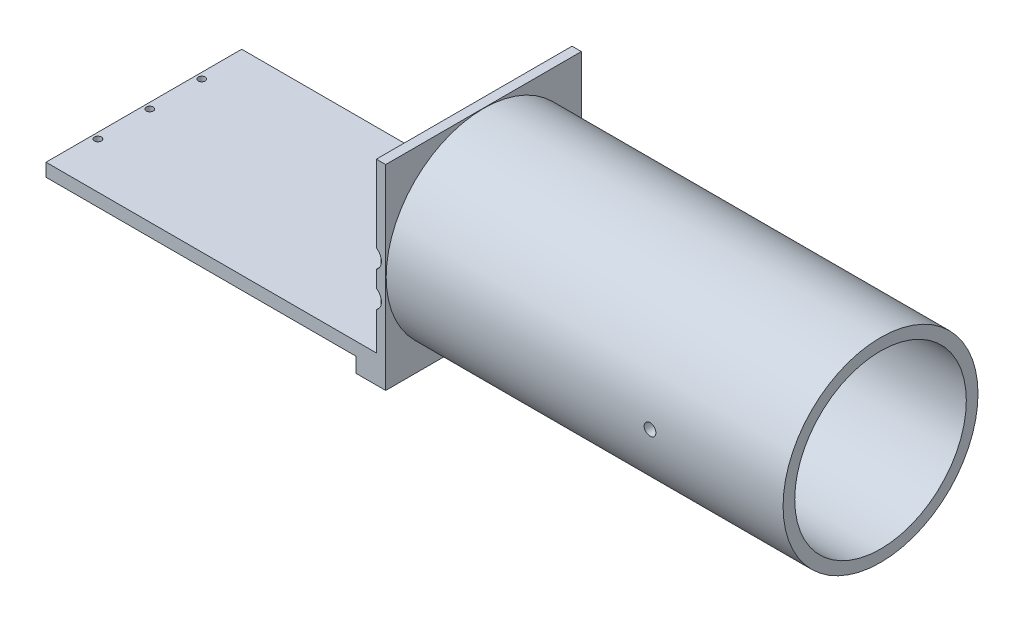
SolidWorks part; units mm, degrees
ref_plane "Front Plane" through (0, 0, 0) normal (0, 0, 1) x (1, 0, 0)
ref_plane "Top Plane" through (0, 0, 0) normal (0, 1, 0) x (1, 0, 0)
ref_plane "Right Plane" through (0, 0, 0) normal (1, 0, 0) x (0, 0, -1)
sketch "Sketch3" plane through (0, 0, 0) normal (0, 1, 0) x (1, 0, 0)
  line L0 (-38.8297, 34.4457) -> (-38.8297, -49.3743)
  line L1 (-38.8297, -49.3743) -> (106.6703, -49.3743)
  line L2 (106.6703, -49.3743) -> (106.6703, 34.4457)
  line L3 (106.6703, 34.4457) -> (-38.8297, 34.4457)
  dimension "D1" = 83.82
  dimension "D2" = 145.5
extrude "Boss-Extrude1" add sketch "Sketch3" along normal blind 83.82
sketch "Sketch4" plane through (0, 83.82, 0) normal (0, 1, 0) x (1, 0, 0)
  line L0 (-38.8297, 34.4457) -> (-38.8297, -44.8663)
  line L1 (-38.8297, 34.4457) -> (-38.8297, -49.3743) construction
  line L2 (-38.8297, -44.8663) -> (102.6703, -44.8663)
  line L3 (102.6703, -44.8663) -> (102.6703, 34.4457)
  line L4 (106.6703, 34.4457) -> (-38.8297, 34.4457) construction
  line L5 (102.6703, 34.4457) -> (-38.8297, 34.4457)
  dimension "D1" = 79.312
  dimension "D2" = 141.5
extrude "Cut-Extrude1" cut sketch "Sketch4" against normal blind 71.882
sketch "Sketch5" plane through (106.6703, 0, 0) normal (1, 0, 0) x (0, 0, -1)
  line L0 (-32.4113, 83.82) -> (-32.4113, 11.938) construction
  line L1 (-44.8663, 83.82) -> (34.4457, 83.82) construction
  line L2 (-44.8663, 11.938) -> (34.4457, 11.938) construction
  line L3 (-7.4113, 83.82) -> (-7.4113, 11.938) construction
  line L4 (17.5887, 83.82) -> (17.5887, 11.938) construction
  line L5 (34.4457, 54.438) -> (-44.8663, 54.438) construction
  line L6 (34.4457, 11.938) -> (34.4457, 83.82) construction
  line L7 (-44.8663, 11.938) -> (-44.8663, 83.82) construction
  line L8 (34.4457, 41.938) -> (-44.8663, 41.938) construction
  line L9 (34.4457, 29.438) -> (-44.8663, 29.438) construction
  line L10 (-44.8663, 11.938) -> (-44.8663, 83.82) construction
  line L11 (34.4457, 11.938) -> (-44.8663, 11.938) construction
  circle A0 centre (-7.4113, 41.938) radius 12.7
  dimension "D1" = 12.455
  dimension "D2" = 37.455
  dimension "D3" = 62.455
  dimension "D4" = 17.5
  dimension "D5" = 30
  dimension "D6" = 42.5
hole_wizard "CBORE for M3 Hex Head Cap Screw1" positions "Sketch6" profile "Sketch7" counterbore size "M3" standard "ISO" end condition up to next
sketch "Sketch6" plane through (106.6703, 0, 0) normal (1, 0, 0) x (0, 0, -1)
  line L0 (-32.4113, 83.82) -> (-32.4113, 11.938) construction
  line L1 (34.4457, 54.438) -> (-44.8663, 54.438) construction
  line L2 (17.5887, 83.82) -> (17.5887, 11.938) construction
  line L3 (34.4457, 29.438) -> (-44.8663, 29.438) construction
  point P0 (-32.4113, 54.438)
  point P6 (17.5887, 54.438)
  point P10 (17.5887, 29.438)
  point P14 (-32.4113, 29.438)
sketch "Sketch7" plane through (106.6703, 54.438, 32.4113) normal (0, 1, 0) x (0, 0, -1)
  line L0 (0, 0) -> (0, 4)
  line L1 (0, 4) -> (1.7, 4)
  line L3 (1.7, 4) -> (1.7, 2)
  line L4 (1.7, 2) -> (4.6755, 2)
  line L5 (4.6755, 2) -> (4.6755, 0)
  line L7 (4.6755, 0) -> (0, 0)
  line L11 (0, -6.35) -> (0, 107.95) construction
  dimension "Thru Hole Dia." = 3.4
  dimension "Thru Hole Depth" = 4
  dimension "C'Bore Dia." = 9.351
  dimension "C'Bore Depth" = 2
extrude "Cut-Extrude3" cut sketch "Sketch5" against normal up to next contours A0
sketch "Sketch8" plane through (0, 0, 49.3743) normal (0, 0, 1) x (1, 0, 0)
  line L0 (100.1703, 83.82) -> (100.1703, 11.938) construction
  line L1 (-38.8297, 83.82) -> (102.6703, 83.82) construction
  line L2 (102.6703, 11.938) -> (-38.8297, 11.938) construction
  line L3 (-36.3297, 83.82) -> (-36.3297, 11.938) construction
  line L4 (-38.8297, 11.938) -> (102.6703, 11.938) construction
  line L5 (102.6703, 46.938) -> (-38.8297, 46.938) construction
  line L6 (102.6703, 11.938) -> (102.6703, 83.82) construction
  line L7 (-38.8297, 11.938) -> (-38.8297, 83.82) construction
  line L8 (102.6703, 31.938) -> (-38.8297, 31.938) construction
  line L9 (102.6703, 11.938) -> (102.6703, 83.82) construction
  dimension "D1" = 2.5
  dimension "D2" = 139
  dimension "D3" = 20
  dimension "D4" = 35
hole_wizard "CBORE for M3 Hex Head Cap Screw2" positions "Sketch11" profile "Sketch12" counterbore size "M3" standard "ISO" end condition up to next
sketch "Sketch11" plane through (0, 0, 49.3743) normal (0, 0, 1) x (1, 0, 0)
  line L0 (100.1703, 83.82) -> (100.1703, 11.938) construction
  line L1 (102.6703, 46.938) -> (-38.8297, 46.938) construction
  line L2 (102.6703, 31.938) -> (-38.8297, 31.938) construction
  point P0 (100.1703, 46.938)
  point P6 (100.1703, 31.938)
sketch "Sketch12" plane through (100.1703, 46.938, 49.3743) normal (1, 0, 0) x (0, -1, 0)
  line L0 (0, 0) -> (0, 4.508)
  line L1 (0, 4.508) -> (1.7, 4.508)
  line L3 (1.7, 4.508) -> (1.7, 2)
  line L4 (1.7, 2) -> (4.6755, 2)
  line L5 (4.6755, 2) -> (4.6755, 0)
  line L7 (4.6755, 0) -> (0, 0)
  line L11 (0, -6.35) -> (0, 107.95) construction
  dimension "Thru Hole Dia." = 3.4
  dimension "Thru Hole Depth" = 4.508
  dimension "C'Bore Dia." = 9.351
  dimension "C'Bore Depth" = 2
hole_wizard "Ø3.0mm Dowel Hole1" positions "Sketch13" profile "Sketch14" hole size "Ø3.0" standard "ISO" end condition up to next
sketch "Sketch13" plane through (0, 0, 49.3743) normal (0, 0, 1) x (1, 0, 0)
  line L0 (-36.3297, 83.82) -> (-36.3297, 11.938) construction
  line L1 (102.6703, 46.938) -> (-38.8297, 46.938) construction
  line L2 (102.6703, 31.938) -> (-38.8297, 31.938) construction
  point P0 (-36.3297, 46.938)
  point P6 (-36.3297, 31.938)
sketch "Sketch14" plane through (-36.3297, 46.938, 49.3743) normal (1, 0, 0) x (0, -1, 0)
  line L0 (0, 0) -> (0, 4.508)
  line L1 (0, 4.508) -> (1.5, 4.508)
  line L2 (1.5, 4.508) -> (1.5, 0)
  line L5 (1.5, 0) -> (0, 0)
  line L11 (0, -6.35) -> (0, 107.95) construction
  dimension "Thru Hole Dia." = 3
  dimension "Thru Hole Depth" = 4.508
sketch "Sketch15" plane through (0, 0, 0) normal (0, -1, 0) x (-1, 0, 0)
  line L0 (-100.1703, -44.8663) -> (-100.1703, 34.4457) construction
  line L1 (38.8297, -44.8663) -> (-102.6703, -44.8663) construction
  line L2 (-102.6703, 34.4457) -> (38.8297, 34.4457) construction
  line L3 (36.3297, -44.8663) -> (36.3297, 34.4457) construction
  line L4 (38.8297, -44.8663) -> (-102.6703, -44.8663) construction
  line L5 (-102.6703, -29.6613) -> (38.8297, -29.6613) construction
  line L6 (-102.6703, -44.8663) -> (-102.6703, 34.4457) construction
  line L7 (38.8297, 34.4457) -> (38.8297, -44.8663) construction
  line L8 (-102.6703, -7.4113) -> (38.8297, -7.4113) construction
  line L9 (-102.6703, -44.8663) -> (-102.6703, 34.4457) construction
  line L10 (-102.6703, 14.8387) -> (38.8297, 14.8387) construction
  dimension "D1" = 2.5
  dimension "D2" = 139
  dimension "D3" = 15.205
  dimension "D4" = 37.455
  dimension "D5" = 59.705
hole_wizard "Ø3.0mm Dowel Hole2" positions "Sketch18" profile "Sketch19" hole size "Ø3.0" standard "ISO" end condition up to next
sketch "Sketch18" plane through (0, 0, 0) normal (0, -1, 0) x (-1, 0, 0)
  line L0 (36.3297, -44.8663) -> (36.3297, 34.4457) construction
  line L1 (-102.6703, -29.6613) -> (38.8297, -29.6613) construction
  line L2 (-102.6703, -7.4113) -> (38.8297, -7.4113) construction
  line L3 (-102.6703, 14.8387) -> (38.8297, 14.8387) construction
  point P0 (36.3297, -29.6613)
  point P6 (36.3297, -7.4113)
  point P10 (36.3297, 14.8387)
sketch "Sketch19" plane through (-36.3297, 0, 29.6613) normal (1, 0, 0) x (0, 0, -1)
  line L0 (0, 0) -> (0, 11.938)
  line L1 (0, 11.938) -> (1.5, 11.938)
  line L2 (1.5, 11.938) -> (1.5, 0)
  line L5 (1.5, 0) -> (0, 0)
  line L11 (0, -6.35) -> (0, 107.95) construction
  dimension "Thru Hole Dia." = 3
  dimension "Thru Hole Depth" = 11.938
hole_wizard "CBORE for M3 Hex Head Cap Screw3" positions "Sketch20" profile "Sketch21" counterbore size "M3" standard "ISO" end condition up to next
sketch "Sketch20" plane through (0, 0, 0) normal (0, -1, 0) x (-1, 0, 0)
  line L0 (-100.1703, -44.8663) -> (-100.1703, 34.4457) construction
  line L1 (-102.6703, -29.6613) -> (38.8297, -29.6613) construction
  line L2 (-102.6703, -7.4113) -> (38.8297, -7.4113) construction
  line L3 (-102.6703, 14.8387) -> (38.8297, 14.8387) construction
  point P0 (-100.1703, -29.6613)
  point P6 (-100.1703, -7.4113)
  point P10 (-100.1703, 14.8387)
sketch "Sketch21" plane through (100.1703, 0, 29.6613) normal (1, 0, 0) x (0, 0, -1)
  line L0 (0, 0) -> (0, 11.938)
  line L1 (0, 11.938) -> (1.7, 11.938)
  line L3 (1.7, 11.938) -> (1.7, 2)
  line L4 (1.7, 2) -> (4.6755, 2)
  line L5 (4.6755, 2) -> (4.6755, 0)
  line L7 (4.6755, 0) -> (0, 0)
  line L11 (0, -6.35) -> (0, 107.95) construction
  dimension "Thru Hole Dia." = 3.4
  dimension "Thru Hole Depth" = 11.938
  dimension "C'Bore Dia." = 9.351
  dimension "C'Bore Depth" = 2
sketch "Sketch22" plane through (106.6703, 0, 0) normal (1, 0, 0) x (0, 0, -1)
  circle A0 centre (-7.4113, 41.938) radius 41.75
extrude "Boss-Extrude3" add sketch "Sketch22" along normal blind 170
sketch "Sketch26" plane through (276.6703, 0, 0) normal (1, 0, 0) x (0, 0, -1)
  circle A0 centre (-7.4113, 41.938) radius 36.75
extrude "Cut-Extrude5" cut sketch "Sketch26" against normal up to surface (170 mm away) up to face at (106.6703, 41.938, -34.3387)
sketch "Sketch27" plane through (0, 83.82, 0) normal (0, 1, 0) x (1, 0, 0)
  line L0 (102.6703, -44.8663) -> (102.6703, -49.3743)
  line L1 (-38.8297, -49.3743) -> (106.6703, -49.3743) construction
  line L2 (102.6703, -49.3743) -> (-38.8297, -49.3743)
  line L3 (-38.8297, -49.3743) -> (-38.8297, -44.8663)
  line L4 (-38.8297, -44.8663) -> (102.6703, -44.8663)
extrude "Cut-Extrude7" cut sketch "Sketch27" against normal up to surface (71.882 mm away) up to face at (100.1703, 11.938, 31.3613)
sketch "Sketch28" plane through (0, 0, 0) normal (0, -1, 0) x (-1, 0, 0)
  line L0 (38.8297, -49.3743) -> (38.8297, 34.4457)
  line L1 (38.8297, 34.4457) -> (-93.898, 34.4457)
  line L2 (-106.6703, 34.4457) -> (38.8297, 34.4457) construction
  line L3 (-93.898, 34.4457) -> (-93.898, -49.3743)
  line L4 (38.8297, -49.3743) -> (-106.6703, -49.3743) construction
  line L5 (-93.898, -49.3743) -> (38.8297, -49.3743)
extrude "Cut-Extrude8" cut sketch "Sketch28" against normal blind 6.35
sketch "Sketch32" plane through (276.6703, 0, 0) normal (1, 0, 0) x (0, 0, -1)
  line L0 (34.3387, 41.938) -> (-49.1613, 41.938) construction
  circle A0 centre (-7.4113, 41.938) radius 41.75 construction
sketch "Sketch33" plane through (106.6703, 0, 0) normal (1, 0, 0) x (0, 0, -1)
  line L0 (5.2887, 41.938) -> (-20.1113, 41.938) construction
  line L1 (34.3387, 41.938) -> (-49.1613, 41.938) construction
  circle A0 centre (-7.4113, 41.938) radius 12.7 construction
ref_plane "Plane1" through (0, 41.938, 0) normal (0, -1, 0) x (-1, 0, 0)
sketch "Sketch36" plane through (0, 41.938, 0) normal (0, -1, 0) x (-1, 0, 0)
  line L0 (-191.6703, 34.3387) -> (-191.6703, -49.1613) construction
  line L1 (-106.6703, 34.3387) -> (-276.6703, 34.3387) construction
  line L2 (-276.6703, -49.1613) -> (-106.6703, -49.1613) construction
ref_plane "Plane3" through (191.6703, 41.938, -34.3387) normal (0, 0, -1) x (-1, 0, 0)
sketch "Sketch39" plane through (0, 41.938, 0) normal (0, -1, 0) x (-1, 0, 0)
  line L0 (-219.6703, -49.1613) -> (-219.6703, 34.3387) construction
  line L1 (-276.6703, -49.1613) -> (-106.6703, -49.1613) construction
  line L2 (-106.6703, 34.3387) -> (-276.6703, 34.3387) construction
  line L3 (-191.6703, 34.3387) -> (-191.6703, -49.1613) construction
  dimension "D1" = 28
hole_wizard "Tap Drill for M6 Tap2" positions "Sketch43" profile "Sketch44" hole size "M6" standard "ISO" end condition through all
sketch "Sketch43" plane through (191.6703, 41.938, -34.3387) normal (0, 0, -1) x (-1, 0, 0)
  point P0 (-28, 0)
sketch "Sketch44" plane through (219.6703, 41.938, -34.3387) normal (1, 0, 0) x (0, 1, 0)
  line L0 (0, 0) -> (0, 83.713)
  line L1 (0, 83.713) -> (2.5, 83.713)
  line L2 (2.5, 83.713) -> (2.5, 0)
  line L5 (2.5, 0) -> (0, 0)
  line L11 (0, -6.35) -> (0, 107.95) construction
  dimension "Thru Hole Dia." = 5
  dimension "Thru Hole Depth" = 83.713
